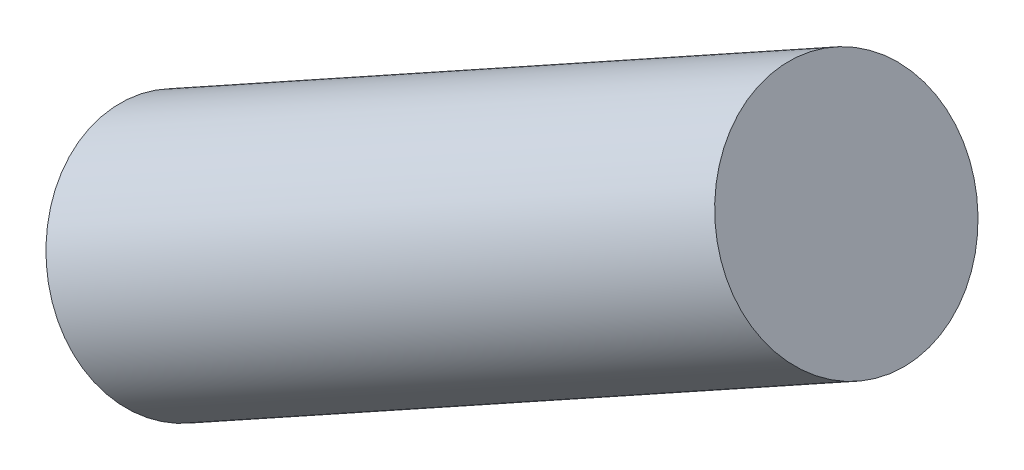
SolidWorks part; units mm, degrees
ref_plane "Front Plane" through (0, 0, 0) normal (0, 0, 1) x (1, 0, 0)
ref_plane "Top Plane" through (0, 0, 0) normal (0, 1, 0) x (1, 0, 0)
ref_plane "Right Plane" through (0, 0, 0) normal (1, 0, 0) x (0, 0, -1)
sketch "Sketch2" plane through (0, 0, 0) normal (0, 0, 1) x (1, 0, 0)
  line L5 (193.3859, 182.0529) -> (-69, 36.61)
  line L6 (-69, 36.61) -> (-129.6012, 145.9375)
  line L7 (193.3859, 182.0529) -> (-69, 36.61)
  dimension "D1" = 0
sweep "Sweep1" add path "Sketch2" circular profile diameter 93 parameters "D3"=93
